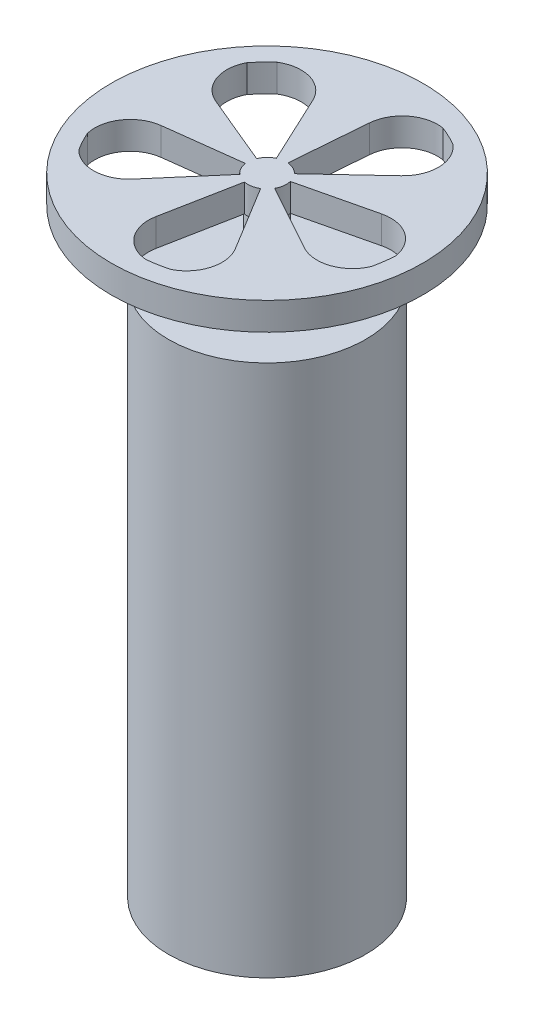
SolidWorks part; units mm, degrees
ref_plane "Front Plane" through (0, 0, 0) normal (0, 0, 1) x (1, 0, 0)
ref_plane "Top Plane" through (0, 0, 0) normal (0, 1, 0) x (1, 0, 0)
ref_plane "Right Plane" through (0, 0, 0) normal (1, 0, 0) x (0, 0, -1)
sketch "Sketch1" plane through (0, 0, 0) normal (0, 1, 0) x (1, 0, 0)
  circle A0 centre (0, 0) radius 25
  dimension "D1" = 50
extrude "Boss-Extrude1" add sketch "Sketch1" along normal blind 10
sketch "Sketch2" plane through (0, 10, 0) normal (0, 1, 0) x (1, 0, 0)
  circle A0 centre (0, 0) radius 22.5
  circle A1 centre (0, 0) radius 25 construction
  circle A2 centre (0, 0) radius 25
  dimension "D1" = 2.5
extrude "Boss-Extrude2" add sketch "Sketch2" along normal blind 120
sketch "Sketch3" plane through (0, 130, 0) normal (0, 1, 0) x (1, 0, 0)
  circle A0 centre (0, 0) radius 25
  circle A1 centre (0, 0) radius 25 construction
  circle A2 centre (0, 0) radius 4.9011
extrude "Boss-Extrude3" add sketch "Sketch3" along normal blind 5
ref_plane "Plane1" through (0, 55, 0) normal (0, 1, 0) x (1, 0, 0)
sketch "Sketch4" plane through (0, 55, 0) normal (0, 1, 0) x (1, 0, 0)
  circle A0 centre (0, 0) radius 10.582
extrude "Boss-Extrude4" add sketch "Sketch4" along normal blind 7 separate body
sketch "Sketch5" plane through (0, 62, 0) normal (0, 1, 0) x (1, 0, 0)
  circle A0 centre (0, 0) radius 3.3942
extrude "Boss-Extrude5" add sketch "Sketch5" along normal blind 90
sketch "Sketch6" plane through (0, 152, 0) normal (0, 1, 0) x (1, 0, 0)
  circle A0 centre (0, 0) radius 3.3942 construction
  circle A1 centre (0, 0) radius 3.3942
  circle A2 centre (0, 0) radius 4.2435
extrude "Boss-Extrude6" add sketch "Sketch6" against normal blind 10
sketch "Sketch8" plane through (0, 152, 0) normal (0, 1, 0) x (1, 0, 0)
  line L0 (0, 0) -> (-22.2749, 9.2826)
  line L1 (0, 0) -> (-10.2006, 21.797)
  line L2 (0, 0) -> (1.9449, 24.0531)
  line L3 (0, 0) -> (17.5781, 16.437)
  line L4 (0, 0) -> (23.4769, 5.5831)
  line L5 (0, 0) -> (21.0644, -11.6384)
  line L6 (0, 0) -> (12.5646, -20.6026)
  line L7 (0, 0) -> (-4.5595, -23.6299)
  line L8 (0, 0) -> (-15.7115, -18.3162)
  line L9 (0, 0) -> (-23.8824, -2.9657)
  circle A0 centre (0, 0) radius 39.5
  arc A1 (-31.5147, -14.0382) -> (-28.9293, -18.7975) centre (0, 0) ccw
  arc A2 (-26.8172, 21.7046) -> (-22.2749, 9.2826) centre (-18.813, 17.5899) ccw
  arc A3 (-23.0897, 25.6343) -> (-10.2006, 21.797) centre (-18.352, 17.9823) cw
  arc A4 (12.3554, 32.2117) -> (1.9449, 24.0531) centre (10.9155, 23.3278) ccw
  arc A5 (17.2445, 29.881) -> (17.5781, 16.437) centre (11.4311, 23.0107) cw
  arc A6 (34.4532, -1.7967) -> (23.4769, 5.5831) centre (25.5591, -3.1726) ccw
  arc A7 (33.7474, -7.1668) -> (21.0644, -11.6384) centre (25.4169, -3.761) cw
  arc A8 (8.9379, -33.3221) -> (12.5646, -20.6026) centre (4.8809, -25.2885) ccw
  arc A9 (3.6125, -34.3103) -> (-4.5595, -23.6299) centre (4.2774, -25.3351) cw
  arc A10 (-28.9293, -18.7975) -> (-15.7115, -18.3162) centre (-22.5426, -12.4566) ccw
  arc A11 (-31.5147, -14.0382) -> (-23.8824, -2.9657) centre (-22.7733, -11.897) cw
  arc A12 (-23.0897, 25.6343) -> (-26.8172, 21.7046) centre (0, 0) ccw
  arc A13 (17.2445, 29.881) -> (12.3554, 32.2117) centre (0, 0) ccw
  arc A14 (33.7474, -7.1668) -> (34.4532, -1.7967) centre (0, 0) ccw
  arc A15 (3.6125, -34.3103) -> (8.9379, -33.3221) centre (0, 0) ccw
  point P31 (0, 0)
  dimension "D2" = 79
  dimension "D3" = 5
  dimension "D1" = 5
extrude "Boss-Extrude7" add sketch "Sketch8" along normal blind 7 separate body contours A0 A15 A9 L7 L8 A10 A1 A11 L9 L0 A2 A12 A3 L1 L2 A4 A13 A5 L3 L4 A6 A14 A7 L5 L6 A8
sketch "Sketch9" plane through (0, 152, 0) normal (0, 1, 0) x (1, 0, 0)
  circle A0 centre (0, 0) radius 4.9011 construction
  circle A1 centre (0, 0) radius 4.9011
extrude "Boss-Extrude8" add sketch "Sketch9" along normal up to surface (7 mm away) up to face at (0, 159, 0)
